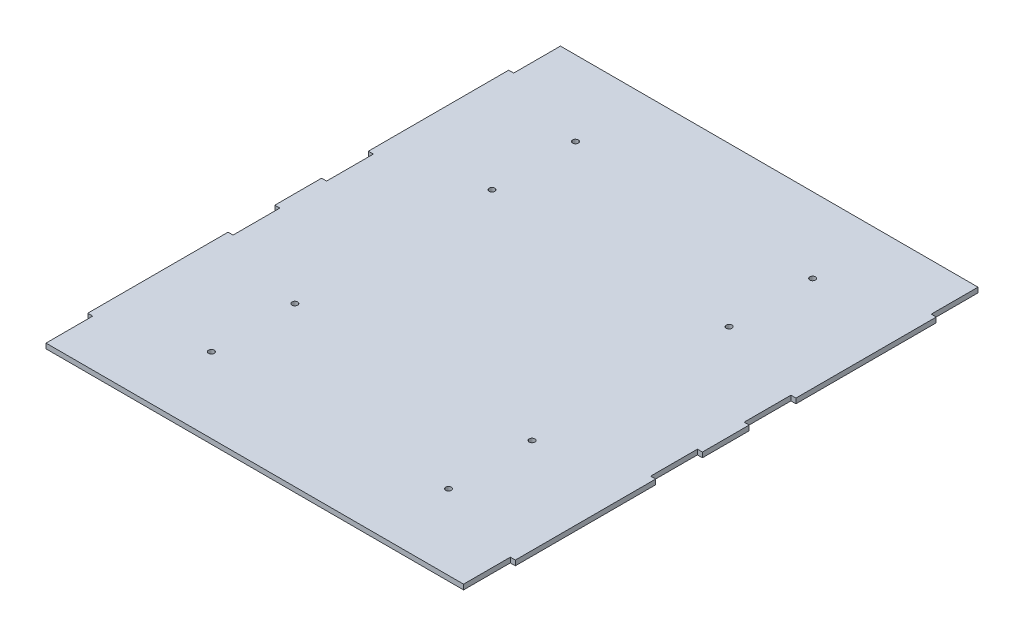
SolidWorks part; units mm, degrees
ref_plane "Alzado" through (0, 0, 0) normal (0, 0, 1) x (1, 0, 0)
ref_plane "Planta" through (0, 0, 0) normal (0, 1, 0) x (1, 0, 0)
ref_plane "Vista lateral" through (0, 0, 0) normal (1, 0, 0) x (0, 0, -1)
sketch "Croquis1" plane through (0, 0, 0) normal (0, 1, 0) x (1, 0, 0)
  line L0 (27.825, -151.749) -> (27.825, 154.0057) construction
  line L1 (-97.175, 154.0057) -> (152.825, 154.0057)
  line L2 (-97.175, 154.0057) -> (-97.175, 126.0057)
  line L3 (-97.175, 126.0057) -> (-100.175, 126.0057)
  line L4 (-100.175, 126.0057) -> (-100.175, 42.0057)
  line L5 (-100.175, 42.0057) -> (-97.175, 42.0057)
  line L6 (-97.175, 42.0057) -> (-97.175, 14.0057)
  line L7 (-97.175, 14.0057) -> (-100.175, 14.0057)
  line L8 (-100.175, 14.0057) -> (-100.175, -13.9943)
  line L9 (-100.175, -13.9943) -> (-97.175, -13.9943)
  line L10 (-97.175, -13.9943) -> (-97.175, -41.9943)
  line L11 (-97.175, -41.9943) -> (-100.175, -41.9943)
  line L12 (-100.175, -41.9943) -> (-100.175, -125.9943)
  line L13 (-100.175, -125.9943) -> (-97.175, -125.9943)
  line L14 (-97.175, -125.9943) -> (-97.175, -153.9943)
  line L29 (-100.175, 84.0057) -> (-30.175, 84.0057) construction
  line L30 (-43.175, 59) -> (-43.175, 109.0114) construction
  line L31 (-100.175, -41.9943) -> (-100.175, -125.9943) construction
  line L33 (-100.175, -83.9943) -> (-30.175, -83.9943) construction
  line L34 (-43.175, -58.9943) -> (-43.175, -108.9943) construction
  line L35 (-97.175, 14.0057) -> (-100.175, 14.0057) construction
  line L36 (-30.175, -71.9943) -> (-30.175, -95.9943) construction
  line L37 (-97.175, -153.9943) -> (152.825, -153.9943)
  line L38 (152.825, 126.0057) -> (155.825, 126.0057)
  line L39 (152.825, 154.0057) -> (152.825, 126.0057)
  line L40 (155.825, 14.0057) -> (155.825, -13.9943)
  line L41 (152.825, 14.0057) -> (155.825, 14.0057)
  line L42 (152.825, 42.0057) -> (152.825, 14.0057)
  line L43 (155.825, 42.0057) -> (152.825, 42.0057)
  line L46 (152.825, -125.9943) -> (152.825, -153.9943)
  line L47 (155.825, -125.9943) -> (152.825, -125.9943)
  line L48 (155.825, -41.9943) -> (155.825, -125.9943)
  line L49 (152.825, -41.9943) -> (155.825, -41.9943)
  line L50 (152.825, -13.9943) -> (152.825, -41.9943)
  line L53 (155.825, 126.0057) -> (155.825, 42.0057)
  line L54 (152.825, -13.9943) -> (155.825, -13.9943)
  circle A0 centre (-43.175, 109.0114) radius 1.7
  circle A1 centre (-43.175, 59) radius 1.7
  circle A2 centre (-43.175, -58.9943) radius 1.7
  circle A3 centre (-43.175, -108.9943) radius 1.7
  circle A4 centre (98.825, 59) radius 1.7
  circle A5 centre (98.825, 109.0114) radius 1.7
  circle A6 centre (98.825, -108.9943) radius 1.7
  circle A7 centre (98.825, -58.9943) radius 1.7
  point P8 (27.825, 154.0057)
  point P30 (-43.175, -83.9943)
  point P38 (-43.175, 84.0057)
  dimension "D1" = 13
  dimension "D2" = 70
  dimension "D3" = 84
extrude "Saliente-Extruir1" add sketch "Croquis1" along normal blind 3
